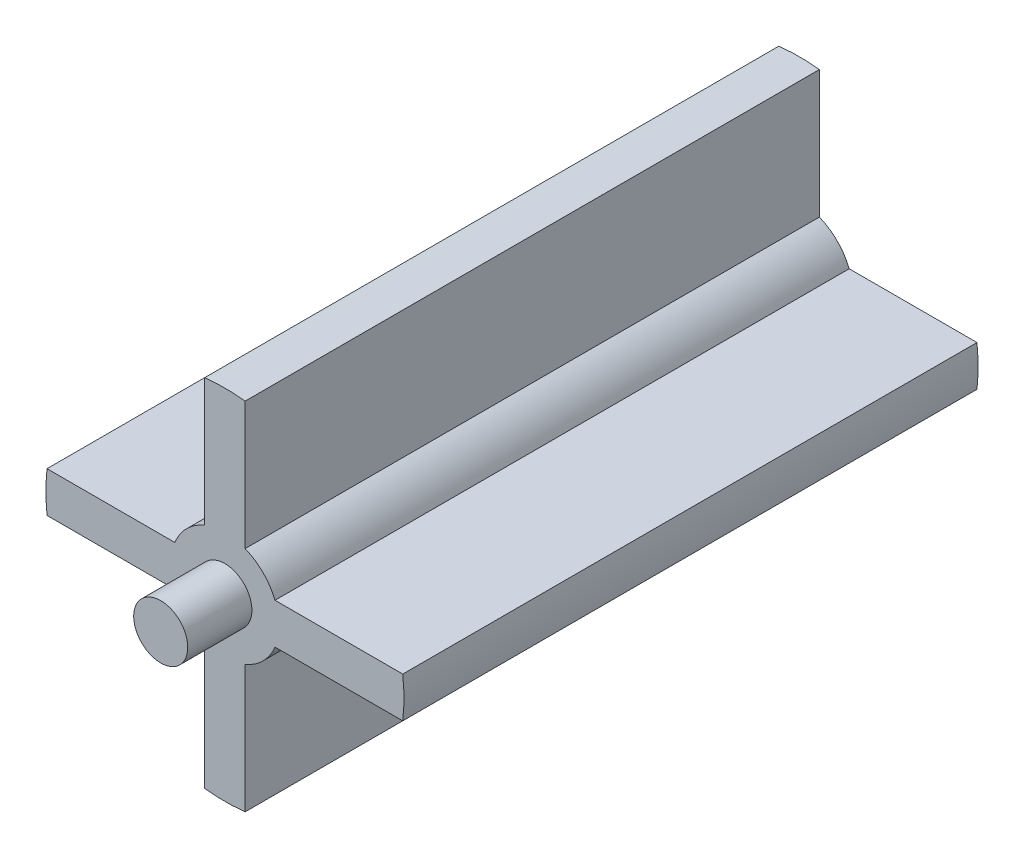
SolidWorks part; units mm, degrees
ref_plane "Front Plane" through (0, 0, 0) normal (0, 0, 1) x (1, 0, 0)
ref_plane "Top Plane" through (0, 0, 0) normal (0, 1, 0) x (1, 0, 0)
ref_plane "Right Plane" through (0, 0, 0) normal (1, 0, 0) x (0, 0, -1)
sketch "Sketch1" plane through (0, 0, 0) normal (0, 0, 1) x (1, 0, 0)
  circle A0 centre (0, 0) radius 26.5
  dimension "D1" = 53
extrude "Boss-Extrude1" add sketch "Sketch1" along normal blind 85
sketch "Sketch2" plane through (0, 0, 85) normal (0, 0, 1) x (1, 0, 0)
  circle A0 centre (0, 0) radius 4
  dimension "D1" = 8
sketch "Sketch3" plane through (0, 0, 0) normal (0, 0, -1) x (-1, 0, 0)
  circle A0 centre (0, 0) radius 4
  dimension "D1" = 8
extrude "Cut-Extrude2" cut sketch "Sketch3" against normal blind 5
sketch "Sketch4" plane through (0, 0, 0) normal (0, 0, -1) x (-1, 0, 0)
  line L0 (0, -26.5) -> (0, -8) construction
  line L1 (8, 0) -> (26.5, 0) construction
  line L2 (0, 7.8049) -> (0, 26.5) construction
  line L3 (-8, 0) -> (-26.5, 0) construction
  line L4 (-26.3296, 3) -> (-7.4162, 3)
  line L6 (-7.4162, -3) -> (-26.3296, -3)
  line L7 (-3, -7.4162) -> (-3, -26.3296)
  line L9 (3, -26.3296) -> (3, -7.4162)
  line L10 (7.4162, 3) -> (26.3296, 3)
  line L12 (26.3296, -3) -> (7.4162, -3)
  line L13 (3, 26.3296) -> (3, 7.4162)
  line L15 (-3, 7.4162) -> (-3, 26.3296)
  arc A0 (-3, 7.4162) -> (-7.4162, 3) centre (0, 0) ccw
  arc A1 (26.3296, -3) -> (26.3296, 3) centre (0, 0) ccw
  circle A2 centre (0, 0) radius 26.5 construction
  arc A3 (-7.4162, -3) -> (-3, -7.4162) centre (0, 0) ccw
  arc A4 (7.4162, 3) -> (3, 7.4162) centre (0, 0) ccw
  arc A5 (3, -7.4162) -> (7.4162, -3) centre (0, 0) ccw
  arc A6 (-3, -26.3296) -> (3, -26.3296) centre (0, 0) ccw
  arc A7 (-26.3296, 3) -> (-26.3296, -3) centre (0, 0) ccw
  arc A8 (3, 26.3296) -> (-3, 26.3296) centre (0, 0) ccw
  dimension "D8" = 8
  dimension "D1" = 3
  dimension "D2" = 3
  dimension "D3" = 3
  dimension "D4" = 3
  dimension "D5" = 3
  dimension "D6" = 3
  dimension "D7" = 3
extrude "Cut-Extrude3" cut sketch "Sketch4" against normal through all flip side to cut
sketch "Sketch5" plane through (0, 0, 0) normal (0, 0, 1) x (1, 0, 0)
  circle A1 centre (9.5329, -9.2187) radius 3.975
  dimension "7.95" = 7.95
extrude "Boss-Extrude2" add sketch "Sketch5" along normal blind 14.5 separate body
extrude "Boss-Extrude3" add sketch "Sketch2" along normal blind 9.5
